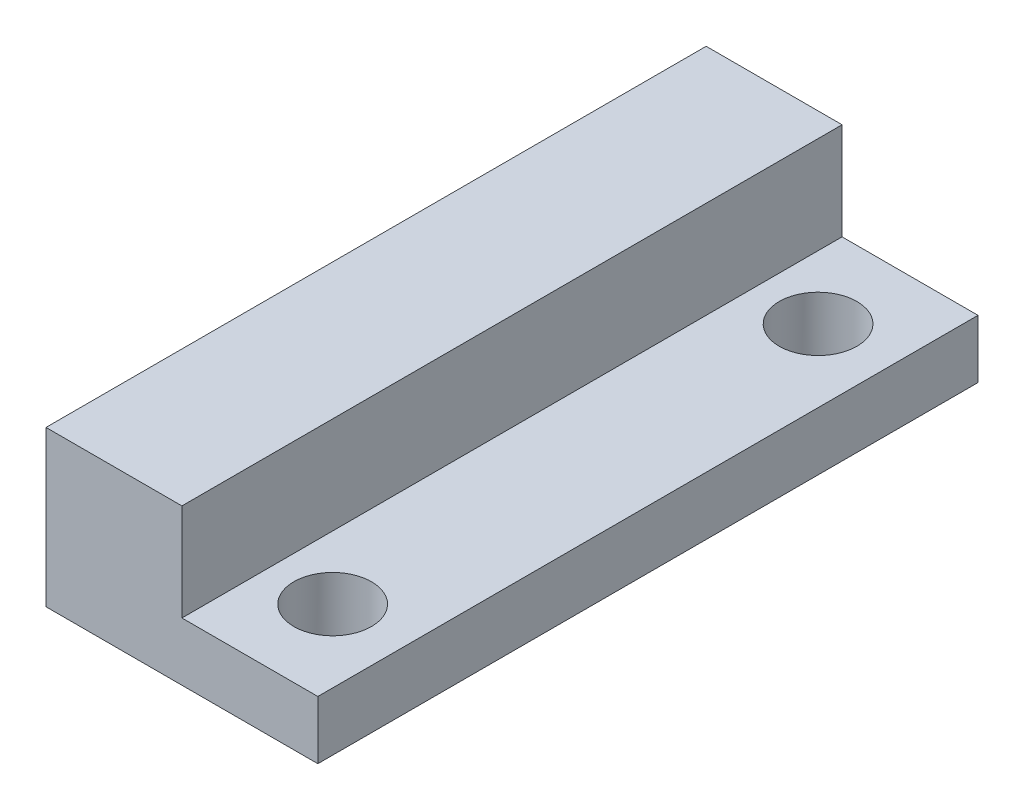
SolidWorks part; units mm, degrees
ref_plane "Front Plane" through (0, 0, 0) normal (0, 0, 1) x (1, 0, 0)
ref_plane "Top Plane" through (0, 0, 0) normal (0, 1, 0) x (1, 0, 0)
ref_plane "Right Plane" through (0, 0, 0) normal (1, 0, 0) x (0, 0, -1)
sketch "Sketch1" plane through (0, 0, 0) normal (0, 1, 0) x (1, 0, 0)
  line L1 (-7, -17) -> (7, -17)
  line L2 (-7, -17) -> (-7, 17)
  line L3 (-7, 17) -> (7, 17)
  line L4 (7, -17) -> (7, 17)
  line L5 (-7, -17) -> (7, 17) construction
  line L6 (-7, 17) -> (7, -17) construction
  point P0 (0, 0)
  dimension "D1" = 34
  dimension "D2" = 14
extrude "Boss-Extrude1" add sketch "Sketch1" along normal blind 3
sketch "Sketch2" plane through (0, 3, 0) normal (0, 1, 0) x (1, 0, 0)
  line L0 (-7, -17) -> (7, -17) construction
  line L1 (-7, 17) -> (0, 17)
  line L2 (-7, 17) -> (-7, -17)
  line L3 (-7, -17) -> (0, -17)
  line L4 (0, 17) -> (0, -17)
  dimension "D1" = 7
extrude "Boss-Extrude2" add sketch "Sketch2" along normal blind 5
sketch "Sketch3" plane through (0, 3, 0) normal (0, 1, 0) x (1, 0, 0)
  line L0 (3.2633, -17) -> (3.2633, 17) construction
  line L1 (0, -17) -> (7, -17) construction
  line L2 (7, 17) -> (0, 17) construction
  line L3 (3.2633, 0) -> (7, 0) construction
  line L4 (7, -17) -> (7, 17) construction
  circle A0 centre (3.2633, -12.5) radius 2
  circle A1 centre (3.2633, 12.5) radius 2
  point P14 (0, 0)
  dimension "D1" = 25
  dimension "D2" = 4
  dimension "D3" = 12.5
extrude "Cut-Extrude1" cut sketch "Sketch3" against normal blind 5
